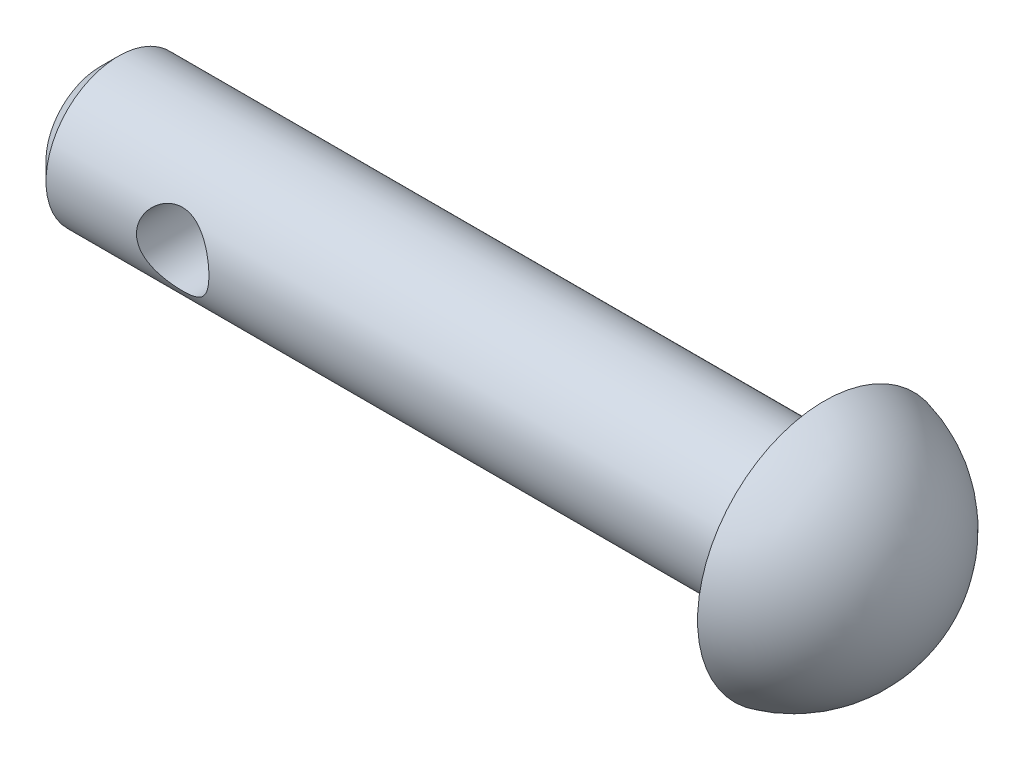
SolidWorks part; units mm, degrees
ref_plane "Front Plane" through (0, 0, 0) normal (0, 0, 1) x (1, 0, 0)
ref_plane "Top Plane" through (0, 0, 0) normal (0, 1, 0) x (1, 0, 0)
ref_plane "Right Plane" through (0, 0, 0) normal (1, 0, 0) x (0, 0, -1)
sketch "Sketch1" plane through (0, 0, 0) normal (1, 0, 0) x (0, 0, -1)
  circle A0 centre (0, 0) radius 2
  dimension "D1" = 4
extrude "Boss-Extrude1" add sketch "Sketch1" against normal blind 20
sketch "Sketch2" plane through (0, 0, 0) normal (0, 0, 1) x (1, 0, 0)
  line L0 (0, -2) -> (0, 2) construction
  circle A0 centre (-16, 0) radius 1
  dimension "D2" = 2
  dimension "D1" = 16
extrude "Cut-Extrude1" cut sketch "Sketch2" against normal through all both and the other way through all
chamfer "Chamfer1" distance 0.5 angle 45 1 edges at (-20, 0, -2)
sketch "Sketch3" plane through (0, 0, 0) normal (0, 1, 0) x (1, 0, 0)
  line L0 (2.7574, 0) -> (0, 0)
  line L1 (0, 0) -> (0, 3.5)
  line L2 (3.3533, 0) -> (-3.0009, 0) construction
  arc A0 (0, 3.5) -> (2.7574, 0) centre (-0.8426, 0) cw
  dimension "D2" = 3.6
  dimension "D1" = 3.5
revolve "Revolve1" add sketch "Sketch3" angle 360 about L2
